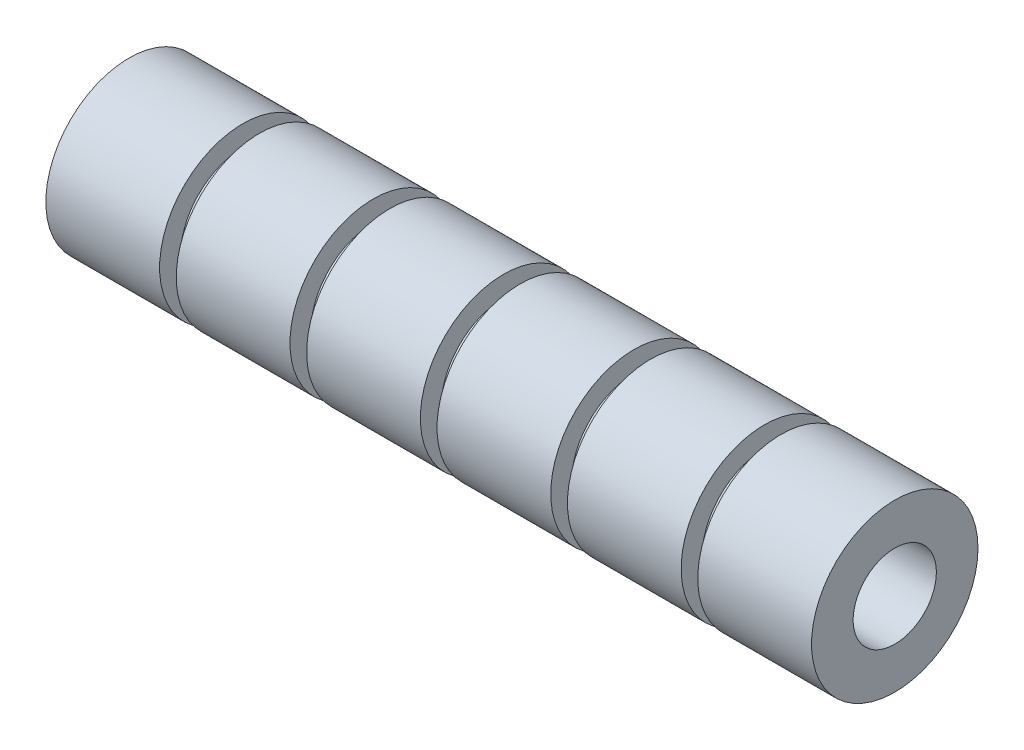
SolidWorks part; units mm, degrees
ref_plane "前基準面" through (0, 0, 0) normal (0, 0, 1) x (1, 0, 0)
ref_plane "上基準面" through (0, 0, 0) normal (0, 1, 0) x (1, 0, 0)
ref_plane "右基準面" through (0, 0, 0) normal (1, 0, 0) x (0, 0, -1)
sketch "草圖1" plane through (0, 0, 0) normal (1, 0, 0) x (0, 0, -1)
  circle A0 centre (0, 0) radius 8.5
  circle A1 centre (0, 0) radius 5
  dimension "D1" = 17
  dimension "D2" = 10
extrude "填料-伸長1" add sketch "草圖1" along normal mid plane 92
sketch "草圖3" plane through (0, 0, 0) normal (0, 0, 1) x (1, 0, 0)
  line L0 (-98.8216, 0) -> (98.8216, 0) construction
  line L1 (46, 8.5) -> (-46, 8.5) construction
  line L2 (30.3333, 8.5) -> (32.3333, 8.5)
  line L3 (30.3333, 8.5) -> (30.3333, 7.5)
  line L4 (30.3333, 7.5) -> (32.3333, 7.5)
  line L5 (32.3333, 8.5) -> (32.3333, 7.5)
  line L6 (14.6667, 8.5) -> (16.6667, 8.5)
  line L7 (14.6667, 8.5) -> (14.6667, 7.5)
  line L8 (14.6667, 7.5) -> (16.6667, 7.5)
  line L9 (16.6667, 8.5) -> (16.6667, 7.5)
  line L10 (-1, 8.5) -> (1, 8.5)
  line L11 (-1, 8.5) -> (-1, 7.5)
  line L12 (-1, 7.5) -> (1, 7.5)
  line L13 (1, 8.5) -> (1, 7.5)
  line L14 (-16.6667, 8.5) -> (-14.6667, 8.5)
  line L15 (-16.6667, 8.5) -> (-16.6667, 7.5)
  line L16 (-16.6667, 7.5) -> (-14.6667, 7.5)
  line L17 (-14.6667, 8.5) -> (-14.6667, 7.5)
  line L18 (-32.3333, 8.5) -> (-30.3333, 8.5)
  line L19 (-32.3333, 8.5) -> (-32.3333, 7.5)
  line L20 (-32.3333, 7.5) -> (-30.3333, 7.5)
  line L21 (-30.3333, 8.5) -> (-30.3333, 7.5)
  point P4 (0, 0)
  point P10 (35.3287, 22.088)
  point P11 (15.1726, 7.5)
  point P28 (0, 0)
  point P29 (-18.4902, 8.5)
  point P30 (0, 8.5)
  point P31 (0, 0)
  point P43 (-4.5919, 0)
  point P44 (-46.5226, 22.4586)
  point P47 (-31.6463, 7.5)
  point P48 (-27.1881, 8.5)
  point P50 (34.6886, 7.5)
  dimension "D1" = 5
  dimension "D2" = 2
  dimension "D3" = 1
  dimension "D4" = 13.6667
revolve "除料-旋轉1" cut sketch "草圖3" angle 360 about L0
sketch "草圖4" plane through (0, 0, 0) normal (0, 0, 1) x (1, 0, 0)
  line L0 (-46, 8.5) -> (-46, -8.5) construction
  line L1 (-32.3333, 8.5) -> (-46, 8.5)
  line L2 (-32.3333, 8.5) -> (-32.3333, 10)
  line L3 (-32.3333, 10) -> (-46, 10)
  line L4 (-46, 8.5) -> (-46, 10)
  line L5 (-16.6667, 8.5) -> (-30.3333, 8.5)
  line L6 (-16.6667, 8.5) -> (-16.6667, 10)
  line L7 (-16.6667, 10) -> (-30.3333, 10)
  line L8 (-30.3333, 8.5) -> (-30.3333, 10)
  line L9 (-1, 8.5) -> (-14.6667, 8.5)
  line L10 (-1, 8.5) -> (-1, 10)
  line L11 (-1, 10) -> (-14.6667, 10)
  line L12 (-14.6667, 8.5) -> (-14.6667, 10)
  line L13 (14.6667, 8.5) -> (1, 8.5)
  line L14 (14.6667, 8.5) -> (14.6667, 10)
  line L15 (14.6667, 10) -> (1, 10)
  line L16 (1, 8.5) -> (1, 10)
  line L17 (30.3333, 8.5) -> (16.6667, 8.5)
  line L18 (30.3333, 8.5) -> (30.3333, 10)
  line L19 (30.3333, 10) -> (16.6667, 10)
  line L20 (16.6667, 8.5) -> (16.6667, 10)
  line L21 (46, 8.5) -> (32.3333, 8.5)
  line L22 (46, 8.5) -> (46, 10)
  line L23 (46, 10) -> (32.3333, 10)
  line L24 (32.3333, 8.5) -> (32.3333, 10)
  line L25 (46, -8.5) -> (46, 8.5) construction
  line L26 (46, 8.5) -> (32.3333, 8.5) construction
  line L27 (58.0898, 0) -> (-58.0898, 0) construction
  point P38 (0, 0)
  dimension "D1" = 6
  dimension "D2" = 20
revolve "旋轉2" add sketch "草圖4" angle 360 about L27
